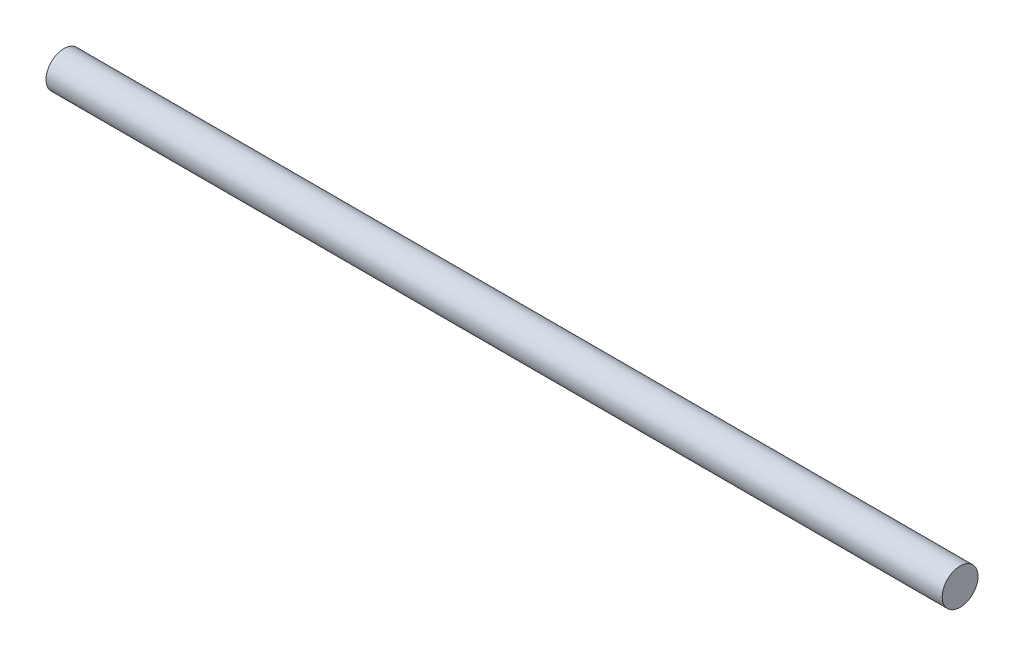
SolidWorks part; units mm, degrees
material "Легированная сталь"
ref_plane "Спереди" through (0, 0, 0) normal (0, 0, 1) x (1, 0, 0)
ref_plane "Сверху" through (0, 0, 0) normal (0, 1, 0) x (1, 0, 0)
ref_plane "Справа" through (0, 0, 0) normal (1, 0, 0) x (0, 0, -1)
sketch "Эскиз1" plane through (0, 0, 0) normal (0, 0, 1) x (1, 0, 0)
  line L0 (-100, 0) -> (100, 0)
  line L1 (-100, 0) -> (-100, 4)
  line L6 (-100, 4) -> (100, 4)
  line L9 (100, 4) -> (100, 0)
  dimension "D1" = 200
  dimension "D8" = 4
revolve "Повернуть1" add sketch "Эскиз1" angle 360 about L0
cosmetic thread "Условное изображение резьбы2" parameters "D2"=6.619
